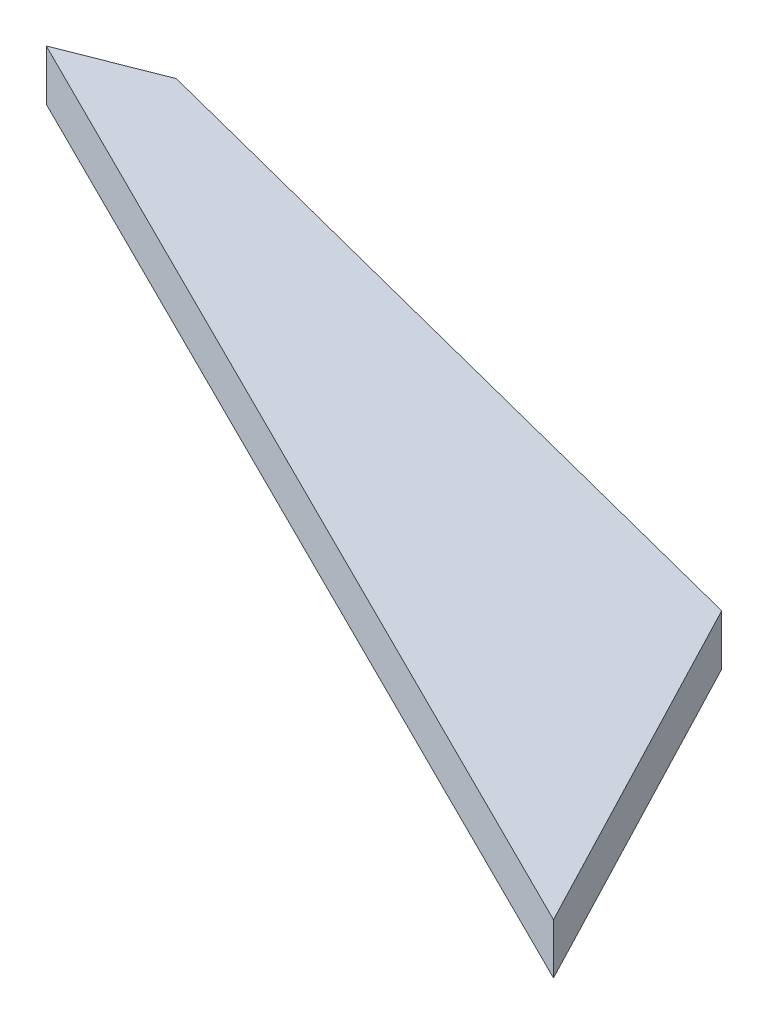
SolidWorks part; units mm, degrees
ref_plane "Plan de face" through (0, 0, 0) normal (0, 0, 1) x (1, 0, 0)
ref_plane "Plan de dessus" through (0, 0, 0) normal (0, 1, 0) x (1, 0, 0)
ref_plane "Plan de droite" through (0, 0, 0) normal (1, 0, 0) x (0, 0, -1)
sketch "Esquisse1" plane through (0, 0, 0) normal (0, 1, 0) x (1, 0, 0)
  line L0 (32.747, -5.9978) -> (3.6875, 1.4577)
  line L1 (3.6875, 1.4577) -> (0, 0)
  line L2 (0, 0) -> (40.0102, -19.9234)
  line L3 (40.0102, -19.9234) -> (32.747, -5.9978)
  point P4 (0, 0)
extrude "Boss.-Extru.1" add sketch "Esquisse1" along normal blind 2
